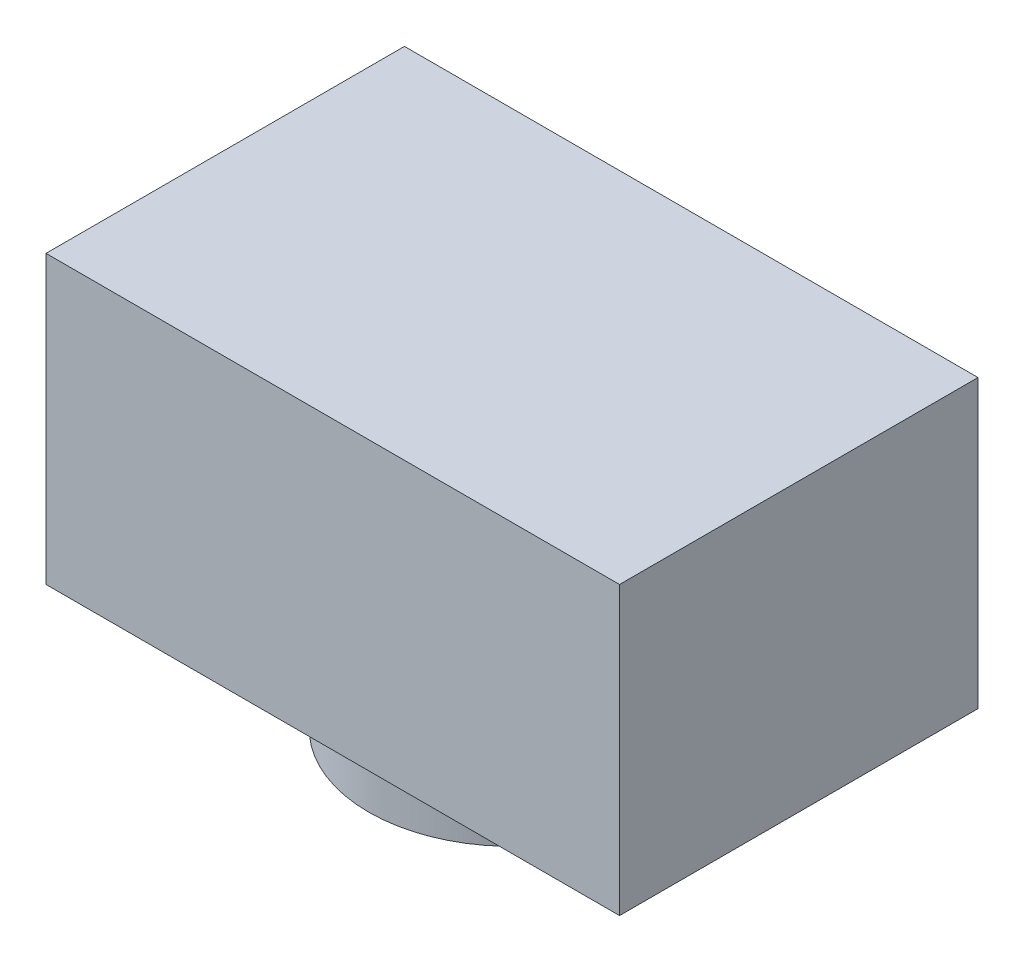
SolidWorks part; units mm, degrees
ref_plane "Front Plane" through (0, 0, 0) normal (0, 0, 1) x (1, 0, 0)
ref_plane "Top Plane" through (0, 0, 0) normal (0, 1, 0) x (1, 0, 0)
ref_plane "Right Plane" through (0, 0, 0) normal (1, 0, 0) x (0, 0, -1)
sketch "Sketch1" plane through (0, 0, 0) normal (0, 0, 1) x (1, 0, 0)
  line L0 (0, -2) -> (0, 2) construction
  line L1 (-4, 2) -> (4, 2)
  line L2 (-4, 2) -> (-4, -2)
  line L3 (-4, -2) -> (4, -2)
  line L4 (4, 2) -> (4, -2)
  line L5 (-4, 2) -> (4, -2) construction
  line L6 (-4, -2) -> (4, 2) construction
  line L7 (4, 0) -> (-4, 0) construction
  point P0 (0, 0)
  dimension "D1" = 4
  dimension "D2" = 8
extrude "Boss-Extrude1" add sketch "Sketch1" along normal blind 5 contours L1 L4 L3 L2
ref_plane "Plane1" through (0, -2, 0) normal (0, -1, 0) x (-1, 0, 0)
sketch "Sketch2" plane through (0, -2, 0) normal (0, -1, 0) x (-1, 0, 0)
  line L0 (0, 0) -> (0, -5) construction
  line L1 (4, 0) -> (-4, 0) construction
  line L2 (4, -5) -> (-4, -5) construction
  line L3 (-4, -2.5) -> (4, -2.5) construction
  line L4 (-4, -5) -> (-4, 0) construction
  line L5 (4, -5) -> (4, 0) construction
  circle A0 centre (0, -2.5) radius 2
  circle A1 centre (0, -2.5) radius 1.9
  circle A2 centre (0, -2.5) radius 1
  circle A3 centre (0, -2.5) radius 0.9
  circle A4 centre (0, -2.5) radius 0.4
  point P19 (0, -2.5)
  dimension "D1" = 4
  dimension "D2" = 3.8
  dimension "D3" = 2
  dimension "D4" = 1.8
  dimension "D5" = 0.8
extrude "Boss-Extrude2" add sketch "Sketch2" along normal blind 1 contours A0
ref_plane "Plane2" through (0, -3, 0) normal (0, -1, 0) x (-1, 0, 0)
sketch "Sketch5" plane through (0, -3, 0) normal (0, -1, 0) x (-1, 0, 0)
  line L0 (0, -4.5) -> (0, -0.5) construction
  line L1 (-2, -2.5) -> (2, -2.5) construction
  circle A0 centre (0, -2.5) radius 2 construction
  circle A1 centre (0, -2.5) radius 1
  dimension "D2" = 2
  dimension "D1" = 4
extrude "Cut-Extrude1" cut sketch "Sketch5" against normal blind 0.25 contours A1
